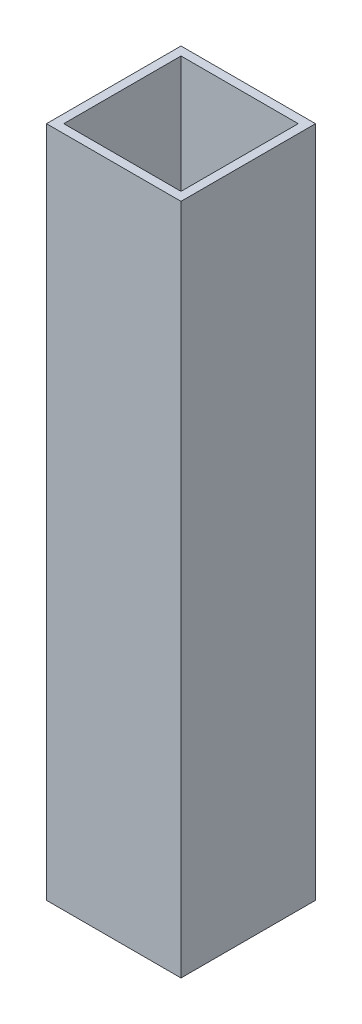
SolidWorks part; units mm, degrees
ref_plane "Front Plane" through (0, 0, 0) normal (0, 0, 1) x (1, 0, 0)
ref_plane "Top Plane" through (0, 0, 0) normal (0, 1, 0) x (1, 0, 0)
ref_plane "Right Plane" through (0, 0, 0) normal (1, 0, 0) x (0, 0, -1)
sketch "Sketch1" plane through (0, 0, 0) normal (0, 1, 0) x (1, 0, 0)
  line L1 (-10, 10) -> (10, 10)
  line L2 (-10, 10) -> (-10, -10)
  line L3 (-10, -10) -> (10, -10)
  line L4 (10, 10) -> (10, -10)
  line L5 (-10, 10) -> (10, -10) construction
  line L6 (-10, -10) -> (10, 10) construction
  line L7 (-8.7158, 8.7158) -> (8.7158, 8.7158)
  line L8 (-8.7158, 8.7158) -> (-8.7158, -8.7158)
  line L9 (-8.7158, -8.7158) -> (8.7158, -8.7158)
  line L10 (8.7158, 8.7158) -> (8.7158, -8.7158)
  line L11 (-8.7158, 8.7158) -> (8.7158, -8.7158) construction
  line L12 (-8.7158, -8.7158) -> (8.7158, 8.7158) construction
  point P0 (0, 0)
  point P6 (0, 0)
  point P11 (8.4605, -8.4605)
  point P12 (8.7158, -8.7158)
  dimension "D1" = 20
  dimension "D2" = 20
extrude "Boss-Extrude1" add sketch "Sketch1" along normal blind 100
